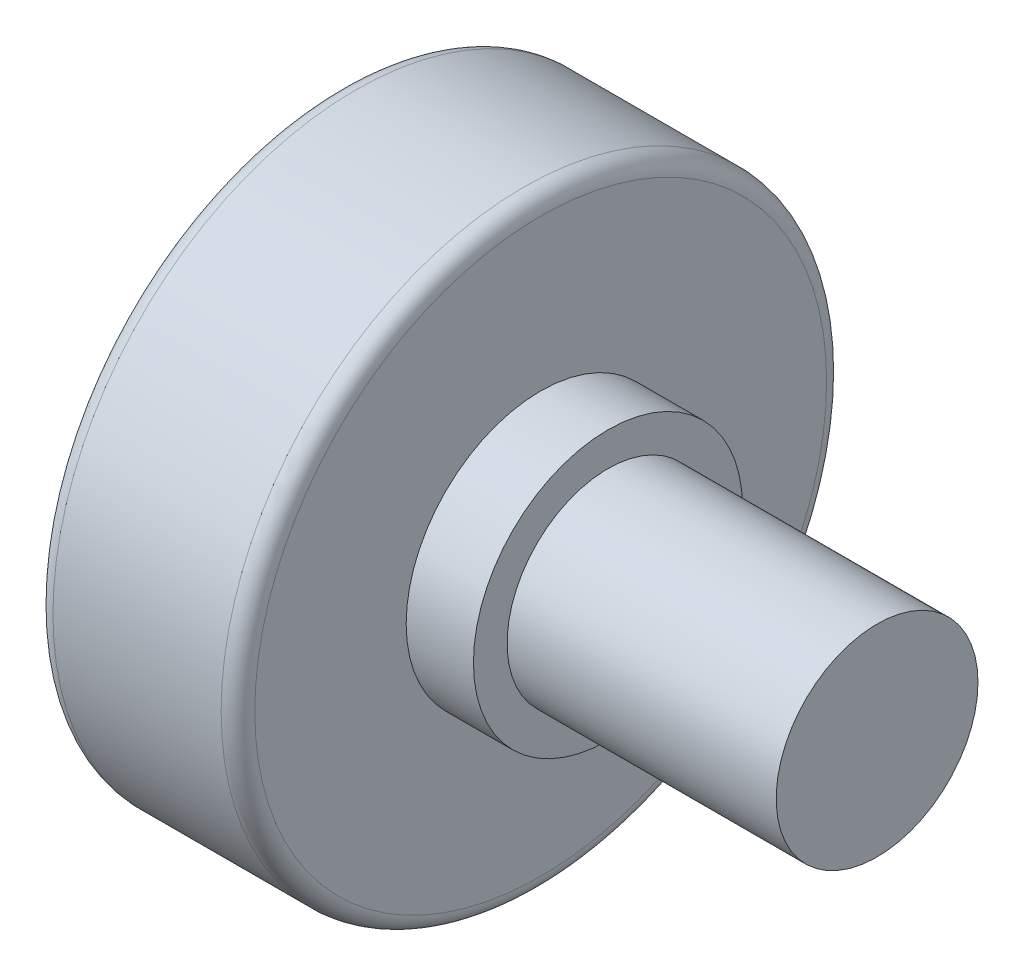
SolidWorks part; units mm, degrees
ref_plane "前视基准面" through (0, 0, 0) normal (0, 0, 1) x (1, 0, 0)
ref_plane "上视基准面" through (0, 0, 0) normal (0, 1, 0) x (1, 0, 0)
ref_plane "右视基准面" through (0, 0, 0) normal (1, 0, 0) x (0, 0, -1)
other "Configuration Table"
sketch "草图1" plane through (0, 0, 0) normal (0, 1, 0) x (1, 0, 0)
  line L0 (0, 0) -> (0, -8.5)
  line L1 (0.5, -9) -> (5.5, -9)
  line L2 (6, -8.5) -> (6, -4)
  line L3 (6, -4) -> (8, -4)
  line L4 (8, -4) -> (8, -3)
  line L5 (8, -3) -> (16, -3)
  line L6 (16, -3) -> (16, 0)
  line L7 (16, 0) -> (0, 0)
  arc A0 (5.5, -9) -> (6, -8.5) centre (5.5, -8.5) ccw
  arc A1 (0, -8.5) -> (0.5, -9) centre (0.5, -8.5) ccw
  dimension "D1" = 0.5
revolve "旋转1" add sketch "草图1" angle 360 about L7
